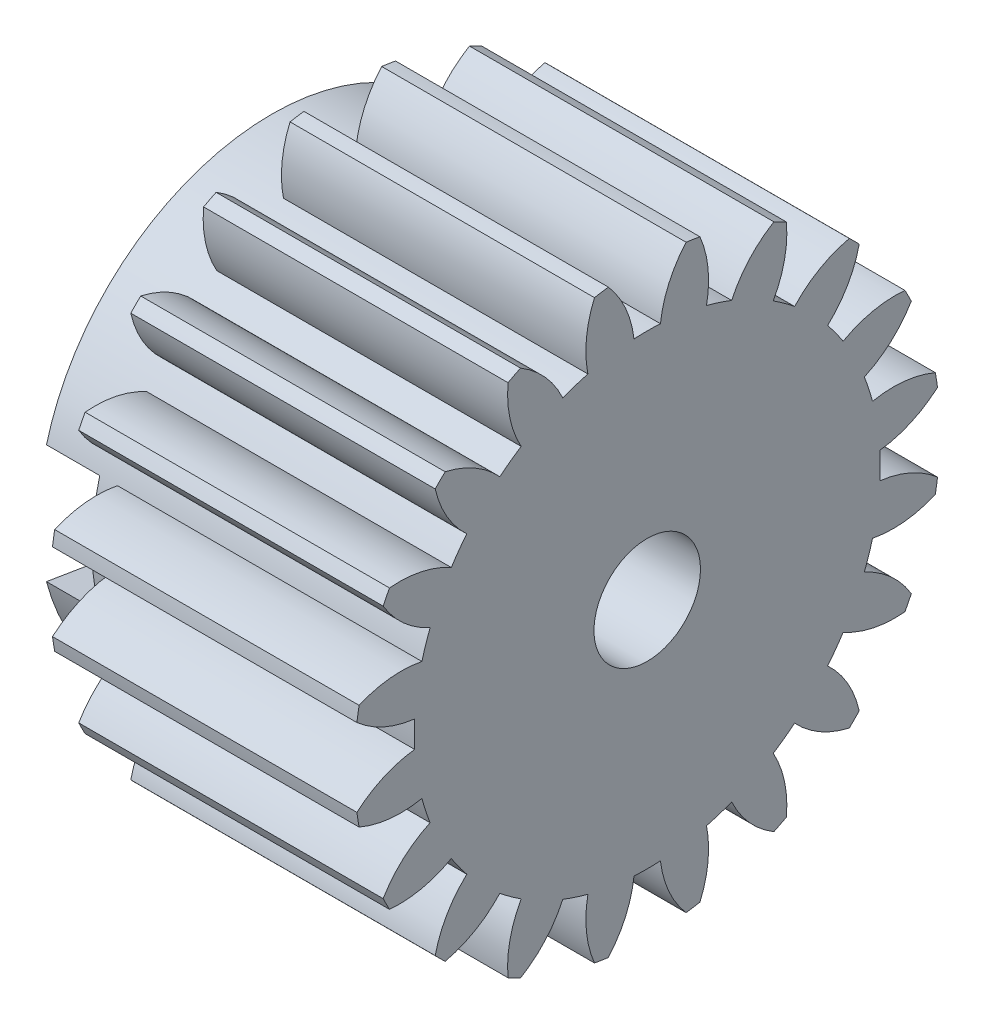
SolidWorks part; units mm, degrees
ref_plane "Plane1" through (0, 0, 0) normal (0, 0, 1) x (1, 0, 0)
ref_plane "Plane2" through (0, 0, 0) normal (0, 1, 0) x (1, 0, 0)
ref_plane "Plane3" through (0, 0, 0) normal (1, 0, 0) x (0, 0, -1)
other "Configuration Table"
sketch "HoldingSke" plane through (0, 0, 0) normal (0, 1, 0) x (1, 0, 0)
  line L0 (0, 0) -> (0.6265, -0.228)
  line L1 (-15, 0) -> (100, 0) construction
  line L2 (0, 0) -> (-2.1039, 2.3779)
  line L3 (0, 0) -> (-11.863, 4.5341)
  line L4 (0, 0) -> (8.1152, 2.9537)
  line L5 (0, 0) -> (-14.9912, -5.5913)
  line L6 (0, 0) -> (-8.2896, -5.593)
  line L7 (-2.1039, 2.3779) -> (1.3401, 18.0029)
  line L8 (-76.2, 54.61) -> (-76.1, 54.61)
  line L9 (-71.009, 38.7566) -> (-53.1078, 45.2721)
  line L10 (-76.2, 71.12) -> (104.1128, 71.12)
  line L11 (0, 0) -> (-10, 0)
  line L12 (-76.2, 101.6) -> (-76.147, 101.6)
  line L13 (24.9733, 27.94) -> (52.9518, 28.4284)
  line L14 (24.9733, 27.94) -> (24.9743, 27.94)
  line L15 (24.9733, 27.94) -> (100.4006, 29.5858)
  line L16 (-63.627, -1.5) -> (-12.827, -1.5)
  circle A0 centre (0, 0) radius 0.4
  circle A1 centre (0, 0) radius 13.124
  circle A2 centre (0, 0) radius 25
  circle A3 centre (0, 0) radius 0.4
  dimension "MHD" = 26.248
  dimension "Hub_dia" = 50
  dimension "Bore" = 0.8
  dimension "MBD" = 0.8
  dimension "Num_teeth" = 20
  dimension "Pitch" = 0.6667
  dimension "Overall_len" = 16
  dimension "Show_teeth" = 20
  dimension "Thickness" = 10
  dimension "OAL" = 16.0001
  dimension "T_dim" = 0.1
  dimension "Ap" = 20
  dimension "H" = 19.05
  dimension "Pitch_radius" = 180.3128
  dimension "Width" = 10
  dimension "Backlash" = 0.053
  dimension "Addendum_fac" = 1
  dimension "Dedendum_fac" = 1.25
  dimension "Clearance_fac" = 0.25
  dimension "Dedendum_add" = 0.001
  dimension "Module" = 1.5
sketch "BasProSke" plane through (0, 0, 0) normal (0, 1, 0) x (1, 0, 0)
  line L0 (-10, 0) -> (60, 0) construction
  line L1 (0, 0) -> (0, 16.5)
  line L2 (0, 0) -> (10, 0)
  line L3 (10, 0) -> (10, 16.5)
  line L4 (10, 16.5) -> (0, 16.5)
  dimension "Thickness" = 10
  dimension "Diameter" = 33
revolve "Base-Revolve" add sketch "BasProSke" angle 360 about L0
sketch "TooCutSke" plane through (0, 0, 0) normal (1, 0, 0) x (0, 0, -1)
  line L1 (0, 0) -> (0, 107) construction
  line L2 (0, 0) -> (-1.2696, 14.9462) construction
  line L3 (0, 0) -> (-4.6808, 29.5532) construction
  line L4 (-1.2696, 14.9462) -> (-2.3404, 14.7766) construction
  arc A0 (0.7438, 13.1029) -> (-0.7438, 13.1029) centre (0, 0) ccw
  arc A1 (2.21, 16.377) -> (-2.21, 16.377) centre (0, 0) ccw
  circle A2 centre (0, 0) radius 15 construction
  circle A3 centre (0, 0) radius 14.0954 construction
  arc A4 (-0.7438, 13.1029) -> (-2.21, 16.377) centre (-6.7025, 12.3999) ccw
  arc A5 (2.21, 16.377) -> (0.7438, 13.1029) centre (6.7025, 12.3999) ccw
  dimension "Root_dia" = 26.248
  dimension "Overcut_dia" = 33.0508
  dimension "Pitch_dia" = 30
  dimension "Base_dia" = 28.1908
  dimension "Flank_rad" = 6
  dimension "Half_ang" = 9
  dimension "Half_CT" = 1.0841
extrude "ToothCut" cut sketch "TooCutSke" along normal through all
fillet "Breaks" [suppressed] radius 0.03
fillet "RootFillets" [suppressed] radius 0.376
pattern_circular "TeethCuts" count 20 every 18 about axis through (-10, 0, 0) along (1, 0, 0) of "ToothCut", "RootFillets", "Breaks"
sketch "HubNeaOneSke" plane through (0, 0, 0) normal (-1, 0, 0) x (0, 0, 1)
  circle A0 centre (0, 0) radius 13.124
  dimension "Diameter" = 26.248
extrude "HubNearOne" add sketch "HubNeaOneSke" along normal blind 6.0001
sketch "HubNeaBotSke" plane through (0, 0, 0) normal (-1, 0, 0) x (0, 0, 1)
  circle A0 centre (0, 0) radius 13.124
  dimension "Diameter" = 26.248
extrude "HubNearBoth" [suppressed] add sketch "HubNeaBotSke" along normal blind 3
ref_plane "FarPln" through (10, 0, 0) normal (1, 0, 0) x (0, 0, -1)
sketch "HubFarSke" plane through (10, 0, 0) normal (1, 0, 0) x (0, 0, -1)
  circle A0 centre (0, 0) radius 13.124
  dimension "Diameter" = 26.248
extrude "HubFar" [suppressed] add sketch "HubFarSke" along normal blind 3
sketch "BorSke" plane through (0, 0, 0) normal (1, 0, 0) x (0, 0, -1)
  circle A0 centre (0, 0) radius 0.4
  dimension "Diameter" = 0.8
extrude "Bore" cut sketch "BorSke" along normal mid plane 32.0001
sketch "KeySke" plane through (0, 0, 0) normal (1, 0, 0) x (0, 0, -1)
  line L0 (-0.05, 0) -> (-0.05, 0.5)
  line L1 (-0.05, 0.5) -> (0.05, 0.5)
  line L2 (0.05, 0.5) -> (0.05, 0)
  line L3 (0, 0) -> (0, 34) construction
  line L4 (-0.05, 0) -> (0.05, 0)
  dimension "Offset" = 0.5
  dimension "Width" = 0.1
extrude "Keyway" [suppressed] cut sketch "KeySke" along normal mid plane 32.0001
pattern_circular "Keyway2" [suppressed] count 2 every 90 about axis through (-10, 0, 0) along (1, 0, 0)
sketch "Sketch1" plane through (-6.0001, 0, 0) normal (-1, 0, 0) x (0, 0, 1)
  line L0 (0, 0) -> (31.5508, 0) construction
  line L1 (15.95, 2.8) -> (4.4173, 4.7)
  line L2 (15.95, -2.8) -> (4.4173, -4.7)
  line L3 (0, 10.0438) -> (0, -22.686) construction
  line L4 (-15.95, -2.8) -> (-4.4173, -4.7)
  line L5 (-15.95, 2.8) -> (-4.4173, 4.7)
  arc A0 (4.4173, 4.7) -> (-4.4173, 4.7) centre (0, 0) ccw
  circle A1 centre (0, 0) radius 4.25 construction
  arc A2 (15.95, -2.8) -> (15.95, 2.8) centre (15.95, 0) ccw
  arc A3 (-15.95, -2.8) -> (-15.95, 2.8) centre (-15.95, 0) cw
  arc A4 (-4.4173, -4.7) -> (4.4173, -4.7) centre (0, 0) ccw
  point P6 (4.25, 0)
  point P7 (18.75, 0)
  point P8 (4.4173, 4.7)
  point P9 (4.4173, -4.7)
  dimension "D1" = 8.5
  dimension "12.5" = 12.9
  dimension "D2" = 5.6
  dimension "D3" = 14.5
  dimension "D4" = 9.4
extrude "Cut-Extrude1" cut sketch "Sketch1" against normal blind 5
sketch "Sketch2" plane through (10, 0, 0) normal (1, 0, 0) x (0, 0, -1)
  arc A80 (-16.354, 2.1898) -> (-13.1029, 0.7438) centre (-12.3999, 6.7025) ccw
  arc A81 (-13.1029, 0.7438) -> (-13.1029, -0.7438) centre (0, 0) ccw
  arc A82 (-13.1029, -0.7438) -> (-16.354, -2.1898) centre (-12.3999, -6.7025) ccw
  arc A83 (-16.354, -2.1898) -> (-16.2303, -2.9711) centre (0, 0) ccw
  arc A84 (-16.2303, -2.9711) -> (-12.6915, -3.3416) centre (-13.8642, 2.5427) ccw
  arc A85 (-12.6915, -3.3416) -> (-12.2318, -4.7564) centre (0, 0) ccw
  arc A86 (-12.2318, -4.7564) -> (-14.8769, -7.1363) centre (-9.7218, -10.2062) ccw
  arc A87 (-14.8769, -7.1363) -> (-14.5178, -7.8411) centre (0, 0) ccw
  arc A88 (-14.5178, -7.8411) -> (-11.0377, -7.0999) centre (-13.9713, -1.866) ccw
  arc A89 (-11.0377, -7.0999) -> (-10.1633, -8.3035) centre (0, 0) ccw
  arc A90 (-10.1633, -8.3035) -> (-11.9436, -11.3842) centre (-6.0921, -12.7109) ccw
  arc A91 (-11.9436, -11.3842) -> (-11.3842, -11.9436) centre (0, 0) ccw
  arc A92 (-11.3842, -11.9436) -> (-8.3035, -10.1633) centre (-12.7109, -6.0921) ccw
  arc A93 (-8.3035, -10.1633) -> (-7.0999, -11.0377) centre (0, 0) ccw
  arc A94 (-7.0999, -11.0377) -> (-7.8411, -14.5178) centre (-1.866, -13.9713) ccw
  arc A95 (-7.8411, -14.5178) -> (-7.1363, -14.8769) centre (0, 0) ccw
  arc A96 (-7.1363, -14.8769) -> (-4.7564, -12.2318) centre (-10.2062, -9.7218) ccw
  arc A97 (-4.7564, -12.2318) -> (-3.3416, -12.6915) centre (0, 0) ccw
  arc A98 (-3.3416, -12.6915) -> (-2.9711, -16.2303) centre (2.5427, -13.8642) ccw
  arc A99 (-2.9711, -16.2303) -> (-2.1898, -16.354) centre (0, 0) ccw
  arc A100 (-2.1898, -16.354) -> (-0.7438, -13.1029) centre (-6.7025, -12.3999) ccw
  arc A101 (-0.7438, -13.1029) -> (0.7438, -13.1029) centre (0, 0) ccw
  arc A102 (0.7438, -13.1029) -> (2.1898, -16.354) centre (6.7025, -12.3999) ccw
  arc A103 (2.1898, -16.354) -> (2.9711, -16.2303) centre (0, 0) ccw
  arc A104 (2.9711, -16.2303) -> (3.3416, -12.6915) centre (-2.5427, -13.8642) ccw
  arc A105 (3.3416, -12.6915) -> (4.7564, -12.2318) centre (0, 0) ccw
  arc A106 (4.7564, -12.2318) -> (7.1363, -14.8769) centre (10.2062, -9.7218) ccw
  arc A107 (7.1363, -14.8769) -> (7.8411, -14.5178) centre (0, 0) ccw
  arc A108 (7.8411, -14.5178) -> (7.0999, -11.0377) centre (1.866, -13.9713) ccw
  arc A109 (7.0999, -11.0377) -> (8.3035, -10.1633) centre (0, 0) ccw
  arc A110 (8.3035, -10.1633) -> (11.3842, -11.9436) centre (12.7109, -6.0921) ccw
  arc A111 (11.3842, -11.9436) -> (11.9436, -11.3842) centre (0, 0) ccw
  arc A112 (11.9436, -11.3842) -> (10.1633, -8.3035) centre (6.0921, -12.7109) ccw
  arc A113 (10.1633, -8.3035) -> (11.0377, -7.0999) centre (0, 0) ccw
  arc A114 (11.0377, -7.0999) -> (14.5178, -7.8411) centre (13.9713, -1.866) ccw
  arc A115 (14.5178, -7.8411) -> (14.8769, -7.1363) centre (0, 0) ccw
  arc A116 (14.8769, -7.1363) -> (12.2318, -4.7564) centre (9.7218, -10.2062) ccw
  arc A117 (12.2318, -4.7564) -> (12.6915, -3.3416) centre (0, 0) ccw
  arc A118 (12.6915, -3.3416) -> (16.2303, -2.9711) centre (13.8642, 2.5427) ccw
  arc A119 (16.2303, -2.9711) -> (16.354, -2.1898) centre (0, 0) ccw
  arc A120 (16.354, -2.1898) -> (13.1029, -0.7438) centre (12.3999, -6.7025) ccw
  arc A121 (13.1029, -0.7438) -> (13.1029, 0.7438) centre (0, 0) ccw
  arc A122 (13.1029, 0.7438) -> (16.354, 2.1898) centre (12.3999, 6.7025) ccw
  arc A123 (16.354, 2.1898) -> (16.2303, 2.9711) centre (0, 0) ccw
  arc A124 (16.2303, 2.9711) -> (12.6915, 3.3416) centre (13.8642, -2.5427) ccw
  arc A125 (12.6915, 3.3416) -> (12.2318, 4.7564) centre (0, 0) ccw
  arc A126 (12.2318, 4.7564) -> (14.8769, 7.1363) centre (9.7218, 10.2062) ccw
  arc A127 (14.8769, 7.1363) -> (14.5178, 7.8411) centre (0, 0) ccw
  arc A128 (14.5178, 7.8411) -> (11.0377, 7.0999) centre (13.9713, 1.866) ccw
  arc A129 (11.0377, 7.0999) -> (10.1633, 8.3035) centre (0, 0) ccw
  arc A130 (10.1633, 8.3035) -> (11.9436, 11.3842) centre (6.0921, 12.7109) ccw
  arc A131 (11.9436, 11.3842) -> (11.3842, 11.9436) centre (0, 0) ccw
  arc A132 (11.3842, 11.9436) -> (8.3035, 10.1633) centre (12.7109, 6.0921) ccw
  arc A133 (8.3035, 10.1633) -> (7.0999, 11.0377) centre (0, 0) ccw
  arc A134 (7.0999, 11.0377) -> (7.8411, 14.5178) centre (1.866, 13.9713) ccw
  arc A135 (7.8411, 14.5178) -> (7.1363, 14.8769) centre (0, 0) ccw
  arc A136 (7.1363, 14.8769) -> (4.7564, 12.2318) centre (10.2062, 9.7218) ccw
  arc A137 (4.7564, 12.2318) -> (3.3416, 12.6915) centre (0, 0) ccw
  arc A138 (3.3416, 12.6915) -> (2.9711, 16.2303) centre (-2.5427, 13.8642) ccw
  arc A139 (2.9711, 16.2303) -> (2.1898, 16.354) centre (0, 0) ccw
  arc A140 (2.1898, 16.354) -> (0.7438, 13.1029) centre (6.7025, 12.3999) ccw
  arc A141 (0.7438, 13.1029) -> (-0.7438, 13.1029) centre (0, 0) ccw
  arc A142 (-0.7438, 13.1029) -> (-2.1898, 16.354) centre (-6.7025, 12.3999) ccw
  arc A143 (-2.1898, 16.354) -> (-2.9711, 16.2303) centre (0, 0) ccw
  arc A144 (-2.9711, 16.2303) -> (-3.3416, 12.6915) centre (2.5427, 13.8642) ccw
  arc A145 (-3.3416, 12.6915) -> (-4.7564, 12.2318) centre (0, 0) ccw
  arc A146 (-4.7564, 12.2318) -> (-7.1363, 14.8769) centre (-10.2062, 9.7218) ccw
  arc A147 (-7.1363, 14.8769) -> (-7.8411, 14.5178) centre (0, 0) ccw
  arc A148 (-7.8411, 14.5178) -> (-7.0999, 11.0377) centre (-1.866, 13.9713) ccw
  arc A149 (-7.0999, 11.0377) -> (-8.3035, 10.1633) centre (0, 0) ccw
  arc A150 (-8.3035, 10.1633) -> (-11.3842, 11.9436) centre (-12.7109, 6.0921) ccw
  arc A151 (-11.3842, 11.9436) -> (-11.9436, 11.3842) centre (0, 0) ccw
  arc A152 (-11.9436, 11.3842) -> (-10.1633, 8.3035) centre (-6.0921, 12.7109) ccw
  arc A153 (-10.1633, 8.3035) -> (-11.0377, 7.0999) centre (0, 0) ccw
  arc A154 (-11.0377, 7.0999) -> (-14.5178, 7.8411) centre (-13.9713, 1.866) ccw
  arc A155 (-14.5178, 7.8411) -> (-14.8769, 7.1363) centre (0, 0) ccw
  arc A156 (-14.8769, 7.1363) -> (-12.2318, 4.7564) centre (-9.7218, 10.2062) ccw
  arc A157 (-12.2318, 4.7564) -> (-12.6915, 3.3416) centre (0, 0) ccw
  arc A158 (-12.6915, 3.3416) -> (-16.2303, 2.9711) centre (-13.8642, -2.5427) ccw
  arc A159 (-16.2303, 2.9711) -> (-16.354, 2.1898) centre (0, 0) ccw
  arc A160 (-16.354, 2.1898) -> (-13.1029, 0.7438) centre (-12.3999, 6.7025) ccw
  arc A161 (-13.1029, 0.7438) -> (-13.1029, -0.7438) centre (0, 0) ccw
  arc A162 (-13.1029, -0.7438) -> (-16.354, -2.1898) centre (-12.3999, -6.7025) ccw
  arc A163 (-16.354, -2.1898) -> (-16.2303, -2.9711) centre (0, 0) ccw
  arc A164 (-16.2303, -2.9711) -> (-12.6915, -3.3416) centre (-13.8642, 2.5427) ccw
  arc A165 (-12.6915, -3.3416) -> (-12.2318, -4.7564) centre (0, 0) ccw
  arc A166 (-12.2318, -4.7564) -> (-14.8769, -7.1363) centre (-9.7218, -10.2062) ccw
  arc A167 (-14.8769, -7.1363) -> (-14.5178, -7.8411) centre (0, 0) ccw
  arc A168 (-14.5178, -7.8411) -> (-11.0377, -7.0999) centre (-13.9713, -1.866) ccw
  arc A169 (-11.0377, -7.0999) -> (-10.1633, -8.3035) centre (0, 0) ccw
  arc A170 (-10.1633, -8.3035) -> (-11.9436, -11.3842) centre (-6.0921, -12.7109) ccw
  arc A171 (-11.9436, -11.3842) -> (-11.3842, -11.9436) centre (0, 0) ccw
  arc A172 (-11.3842, -11.9436) -> (-8.3035, -10.1633) centre (-12.7109, -6.0921) ccw
  arc A173 (-8.3035, -10.1633) -> (-7.0999, -11.0377) centre (0, 0) ccw
  arc A174 (-7.0999, -11.0377) -> (-7.8411, -14.5178) centre (-1.866, -13.9713) ccw
  arc A175 (-7.8411, -14.5178) -> (-7.1363, -14.8769) centre (0, 0) ccw
  arc A176 (-7.1363, -14.8769) -> (-4.7564, -12.2318) centre (-10.2062, -9.7218) ccw
  arc A177 (-4.7564, -12.2318) -> (-3.3416, -12.6915) centre (0, 0) ccw
  arc A178 (-3.3416, -12.6915) -> (-2.9711, -16.2303) centre (2.5427, -13.8642) ccw
  arc A179 (-2.9711, -16.2303) -> (-2.1898, -16.354) centre (0, 0) ccw
  arc A180 (-2.1898, -16.354) -> (-0.7438, -13.1029) centre (-6.7025, -12.3999) ccw
  arc A181 (-0.7438, -13.1029) -> (0.7438, -13.1029) centre (0, 0) ccw
  arc A182 (0.7438, -13.1029) -> (2.1898, -16.354) centre (6.7025, -12.3999) ccw
  arc A183 (2.1898, -16.354) -> (2.9711, -16.2303) centre (0, 0) ccw
  arc A184 (2.9711, -16.2303) -> (3.3416, -12.6915) centre (-2.5427, -13.8642) ccw
  arc A185 (3.3416, -12.6915) -> (4.7564, -12.2318) centre (0, 0) ccw
  arc A186 (4.7564, -12.2318) -> (7.1363, -14.8769) centre (10.2062, -9.7218) ccw
  arc A187 (7.1363, -14.8769) -> (7.8411, -14.5178) centre (0, 0) ccw
  arc A188 (7.8411, -14.5178) -> (7.0999, -11.0377) centre (1.866, -13.9713) ccw
  arc A189 (7.0999, -11.0377) -> (8.3035, -10.1633) centre (0, 0) ccw
  arc A190 (8.3035, -10.1633) -> (11.3842, -11.9436) centre (12.7109, -6.0921) ccw
  arc A191 (11.3842, -11.9436) -> (11.9436, -11.3842) centre (0, 0) ccw
  arc A192 (11.9436, -11.3842) -> (10.1633, -8.3035) centre (6.0921, -12.7109) ccw
  arc A193 (10.1633, -8.3035) -> (11.0377, -7.0999) centre (0, 0) ccw
  arc A194 (11.0377, -7.0999) -> (14.5178, -7.8411) centre (13.9713, -1.866) ccw
  arc A195 (14.5178, -7.8411) -> (14.8769, -7.1363) centre (0, 0) ccw
  arc A196 (14.8769, -7.1363) -> (12.2318, -4.7564) centre (9.7218, -10.2062) ccw
  arc A197 (12.2318, -4.7564) -> (12.6915, -3.3416) centre (0, 0) ccw
  arc A198 (12.6915, -3.3416) -> (16.2303, -2.9711) centre (13.8642, 2.5427) ccw
  arc A199 (16.2303, -2.9711) -> (16.354, -2.1898) centre (0, 0) ccw
  arc A200 (16.354, -2.1898) -> (13.1029, -0.7438) centre (12.3999, -6.7025) ccw
  arc A201 (13.1029, -0.7438) -> (13.1029, 0.7438) centre (0, 0) ccw
  arc A202 (13.1029, 0.7438) -> (16.354, 2.1898) centre (12.3999, 6.7025) ccw
  arc A203 (16.354, 2.1898) -> (16.2303, 2.9711) centre (0, 0) ccw
  arc A204 (16.2303, 2.9711) -> (12.6915, 3.3416) centre (13.8642, -2.5427) ccw
  arc A205 (12.6915, 3.3416) -> (12.2318, 4.7564) centre (0, 0) ccw
  arc A206 (12.2318, 4.7564) -> (14.8769, 7.1363) centre (9.7218, 10.2062) ccw
  arc A207 (14.8769, 7.1363) -> (14.5178, 7.8411) centre (0, 0) ccw
  arc A208 (14.5178, 7.8411) -> (11.0377, 7.0999) centre (13.9713, 1.866) ccw
  arc A209 (11.0377, 7.0999) -> (10.1633, 8.3035) centre (0, 0) ccw
  arc A210 (10.1633, 8.3035) -> (11.9436, 11.3842) centre (6.0921, 12.7109) ccw
  arc A211 (11.9436, 11.3842) -> (11.3842, 11.9436) centre (0, 0) ccw
  arc A212 (11.3842, 11.9436) -> (8.3035, 10.1633) centre (12.7109, 6.0921) ccw
  arc A213 (8.3035, 10.1633) -> (7.0999, 11.0377) centre (0, 0) ccw
  arc A214 (7.0999, 11.0377) -> (7.8411, 14.5178) centre (1.866, 13.9713) ccw
  arc A215 (7.8411, 14.5178) -> (7.1363, 14.8769) centre (0, 0) ccw
  arc A216 (7.1363, 14.8769) -> (4.7564, 12.2318) centre (10.2062, 9.7218) ccw
  arc A217 (4.7564, 12.2318) -> (3.3416, 12.6915) centre (0, 0) ccw
  arc A218 (3.3416, 12.6915) -> (2.9711, 16.2303) centre (-2.5427, 13.8642) ccw
  arc A219 (2.9711, 16.2303) -> (2.1898, 16.354) centre (0, 0) ccw
  arc A220 (2.1898, 16.354) -> (0.7438, 13.1029) centre (6.7025, 12.3999) ccw
  arc A221 (0.7438, 13.1029) -> (-0.7438, 13.1029) centre (0, 0) ccw
  arc A222 (-0.7438, 13.1029) -> (-2.1898, 16.354) centre (-6.7025, 12.3999) ccw
  arc A223 (-2.1898, 16.354) -> (-2.9711, 16.2303) centre (0, 0) ccw
  arc A224 (-2.9711, 16.2303) -> (-3.3416, 12.6915) centre (2.5427, 13.8642) ccw
  arc A225 (-3.3416, 12.6915) -> (-4.7564, 12.2318) centre (0, 0) ccw
  arc A226 (-4.7564, 12.2318) -> (-7.1363, 14.8769) centre (-10.2062, 9.7218) ccw
  arc A227 (-7.1363, 14.8769) -> (-7.8411, 14.5178) centre (0, 0) ccw
  arc A228 (-7.8411, 14.5178) -> (-7.0999, 11.0377) centre (-1.866, 13.9713) ccw
  arc A229 (-7.0999, 11.0377) -> (-8.3035, 10.1633) centre (0, 0) ccw
  arc A230 (-8.3035, 10.1633) -> (-11.3842, 11.9436) centre (-12.7109, 6.0921) ccw
  arc A231 (-11.3842, 11.9436) -> (-11.9436, 11.3842) centre (0, 0) ccw
  arc A232 (-11.9436, 11.3842) -> (-10.1633, 8.3035) centre (-6.0921, 12.7109) ccw
  arc A233 (-10.1633, 8.3035) -> (-11.0377, 7.0999) centre (0, 0) ccw
  arc A234 (-11.0377, 7.0999) -> (-14.5178, 7.8411) centre (-13.9713, 1.866) ccw
  arc A235 (-14.5178, 7.8411) -> (-14.8769, 7.1363) centre (0, 0) ccw
  arc A236 (-14.8769, 7.1363) -> (-12.2318, 4.7564) centre (-9.7218, 10.2062) ccw
  arc A237 (-12.2318, 4.7564) -> (-12.6915, 3.3416) centre (0, 0) ccw
  arc A238 (-12.6915, 3.3416) -> (-16.2303, 2.9711) centre (-13.8642, -2.5427) ccw
  arc A239 (-16.2303, 2.9711) -> (-16.354, 2.1898) centre (0, 0) ccw
  dimension "D1" = 0
extrude "Boss-Extrude1" add sketch "Sketch2" along normal blind 7.15 contours A160 A161 A162 A163 A164 A165 A166 A167 A168 A169 A170 A171 A172 A173 A174 A175 A176 A177 A178 A179 A180 A181 A182 A183 A184 A185 A186 A187 A188 A189 A190 A191 A192 A193 A194 A195 A196 A197 A198 A199 A200 A201 A202 A203 A204 A205 A206 A207 A208 A209 A210 A211 A212 A213 A214 A215 A216 A217 A218 A219 A220 A221 A222 A223 A224 A225 A226 A227 A228 A229 A230 A231 A232 A233 A234 A235 A236 A237 A238 A239
sketch "Sketch4" plane through (-6.0001, 0, 0) normal (-1, 0, 0) x (0, 0, 1)
  circle A0 centre (0, 0) radius 13.124
extrude "Cut-Extrude2" cut sketch "Sketch4" against normal blind 2
sketch "Sketch5" plane through (17.15, 0, 0) normal (1, 0, 0) x (0, 0, -1)
  arc A80 (-16.2303, 2.9711) -> (-16.354, 2.1898) centre (0, 0) ccw
  arc A81 (-16.354, 2.1898) -> (-13.1029, 0.7438) centre (-12.3999, 6.7025) ccw
  arc A82 (-13.1029, 0.7438) -> (-13.1029, -0.7438) centre (0, 0) ccw
  arc A83 (-13.1029, -0.7438) -> (-16.354, -2.1898) centre (-12.3999, -6.7025) ccw
  arc A84 (-16.354, -2.1898) -> (-16.2303, -2.9711) centre (0, 0) ccw
  arc A85 (-16.2303, -2.9711) -> (-12.6915, -3.3416) centre (-13.8642, 2.5427) ccw
  arc A86 (-12.6915, -3.3416) -> (-12.2318, -4.7564) centre (0, 0) ccw
  arc A87 (-12.2318, -4.7564) -> (-14.8769, -7.1363) centre (-9.7218, -10.2062) ccw
  arc A88 (-14.8769, -7.1363) -> (-14.5178, -7.8411) centre (0, 0) ccw
  arc A89 (-14.5178, -7.8411) -> (-11.0377, -7.0999) centre (-13.9713, -1.866) ccw
  arc A90 (-11.0377, -7.0999) -> (-10.1633, -8.3035) centre (0, 0) ccw
  arc A91 (-10.1633, -8.3035) -> (-11.9436, -11.3842) centre (-6.0921, -12.7109) ccw
  arc A92 (-11.9436, -11.3842) -> (-11.3842, -11.9436) centre (0, 0) ccw
  arc A93 (-11.3842, -11.9436) -> (-8.3035, -10.1633) centre (-12.7109, -6.0921) ccw
  arc A94 (-8.3035, -10.1633) -> (-7.0999, -11.0377) centre (0, 0) ccw
  arc A95 (-7.0999, -11.0377) -> (-7.8411, -14.5178) centre (-1.866, -13.9713) ccw
  arc A96 (-7.8411, -14.5178) -> (-7.1363, -14.8769) centre (0, 0) ccw
  arc A97 (-7.1363, -14.8769) -> (-4.7564, -12.2318) centre (-10.2062, -9.7218) ccw
  arc A98 (-4.7564, -12.2318) -> (-3.3416, -12.6915) centre (0, 0) ccw
  arc A99 (-3.3416, -12.6915) -> (-2.9711, -16.2303) centre (2.5427, -13.8642) ccw
  arc A100 (-2.9711, -16.2303) -> (-2.1898, -16.354) centre (0, 0) ccw
  arc A101 (-2.1898, -16.354) -> (-0.7438, -13.1029) centre (-6.7025, -12.3999) ccw
  arc A102 (-0.7438, -13.1029) -> (0.7438, -13.1029) centre (0, 0) ccw
  arc A103 (0.7438, -13.1029) -> (2.1898, -16.354) centre (6.7025, -12.3999) ccw
  arc A104 (2.1898, -16.354) -> (2.9711, -16.2303) centre (0, 0) ccw
  arc A105 (2.9711, -16.2303) -> (3.3416, -12.6915) centre (-2.5427, -13.8642) ccw
  arc A106 (3.3416, -12.6915) -> (4.7564, -12.2318) centre (0, 0) ccw
  arc A107 (4.7564, -12.2318) -> (7.1363, -14.8769) centre (10.2062, -9.7218) ccw
  arc A108 (7.1363, -14.8769) -> (7.8411, -14.5178) centre (0, 0) ccw
  arc A109 (7.8411, -14.5178) -> (7.0999, -11.0377) centre (1.866, -13.9713) ccw
  arc A110 (7.0999, -11.0377) -> (8.3035, -10.1633) centre (0, 0) ccw
  arc A111 (8.3035, -10.1633) -> (11.3842, -11.9436) centre (12.7109, -6.0921) ccw
  arc A112 (11.3842, -11.9436) -> (11.9436, -11.3842) centre (0, 0) ccw
  arc A113 (11.9436, -11.3842) -> (10.1633, -8.3035) centre (6.0921, -12.7109) ccw
  arc A114 (10.1633, -8.3035) -> (11.0377, -7.0999) centre (0, 0) ccw
  arc A115 (11.0377, -7.0999) -> (14.5178, -7.8411) centre (13.9713, -1.866) ccw
  arc A116 (14.5178, -7.8411) -> (14.8769, -7.1363) centre (0, 0) ccw
  arc A117 (14.8769, -7.1363) -> (12.2318, -4.7564) centre (9.7218, -10.2062) ccw
  arc A118 (12.2318, -4.7564) -> (12.6915, -3.3416) centre (0, 0) ccw
  arc A119 (12.6915, -3.3416) -> (16.2303, -2.9711) centre (13.8642, 2.5427) ccw
  arc A120 (16.2303, -2.9711) -> (16.354, -2.1898) centre (0, 0) ccw
  arc A121 (16.354, -2.1898) -> (13.1029, -0.7438) centre (12.3999, -6.7025) ccw
  arc A122 (13.1029, -0.7438) -> (13.1029, 0.7438) centre (0, 0) ccw
  arc A123 (13.1029, 0.7438) -> (16.354, 2.1898) centre (12.3999, 6.7025) ccw
  arc A124 (16.354, 2.1898) -> (16.2303, 2.9711) centre (0, 0) ccw
  arc A125 (16.2303, 2.9711) -> (12.6915, 3.3416) centre (13.8642, -2.5427) ccw
  arc A126 (12.6915, 3.3416) -> (12.2318, 4.7564) centre (0, 0) ccw
  arc A127 (12.2318, 4.7564) -> (14.8769, 7.1363) centre (9.7218, 10.2062) ccw
  arc A128 (14.8769, 7.1363) -> (14.5178, 7.8411) centre (0, 0) ccw
  arc A129 (14.5178, 7.8411) -> (11.0377, 7.0999) centre (13.9713, 1.866) ccw
  arc A130 (11.0377, 7.0999) -> (10.1633, 8.3035) centre (0, 0) ccw
  arc A131 (10.1633, 8.3035) -> (11.9436, 11.3842) centre (6.0921, 12.7109) ccw
  arc A132 (11.9436, 11.3842) -> (11.3842, 11.9436) centre (0, 0) ccw
  arc A133 (11.3842, 11.9436) -> (8.3035, 10.1633) centre (12.7109, 6.0921) ccw
  arc A134 (8.3035, 10.1633) -> (7.0999, 11.0377) centre (0, 0) ccw
  arc A135 (7.0999, 11.0377) -> (7.8411, 14.5178) centre (1.866, 13.9713) ccw
  arc A136 (7.8411, 14.5178) -> (7.1363, 14.8769) centre (0, 0) ccw
  arc A137 (7.1363, 14.8769) -> (4.7564, 12.2318) centre (10.2062, 9.7218) ccw
  arc A138 (4.7564, 12.2318) -> (3.3416, 12.6915) centre (0, 0) ccw
  arc A139 (3.3416, 12.6915) -> (2.9711, 16.2303) centre (-2.5427, 13.8642) ccw
  arc A140 (2.9711, 16.2303) -> (2.1898, 16.354) centre (0, 0) ccw
  arc A141 (2.1898, 16.354) -> (0.7438, 13.1029) centre (6.7025, 12.3999) ccw
  arc A142 (0.7438, 13.1029) -> (-0.7438, 13.1029) centre (0, 0) ccw
  arc A143 (-0.7438, 13.1029) -> (-2.1898, 16.354) centre (-6.7025, 12.3999) ccw
  arc A144 (-2.1898, 16.354) -> (-2.9711, 16.2303) centre (0, 0) ccw
  arc A145 (-2.9711, 16.2303) -> (-3.3416, 12.6915) centre (2.5427, 13.8642) ccw
  arc A146 (-3.3416, 12.6915) -> (-4.7564, 12.2318) centre (0, 0) ccw
  arc A147 (-4.7564, 12.2318) -> (-7.1363, 14.8769) centre (-10.2062, 9.7218) ccw
  arc A148 (-7.1363, 14.8769) -> (-7.8411, 14.5178) centre (0, 0) ccw
  arc A149 (-7.8411, 14.5178) -> (-7.0999, 11.0377) centre (-1.866, 13.9713) ccw
  arc A150 (-7.0999, 11.0377) -> (-8.3035, 10.1633) centre (0, 0) ccw
  arc A151 (-8.3035, 10.1633) -> (-11.3842, 11.9436) centre (-12.7109, 6.0921) ccw
  arc A152 (-11.3842, 11.9436) -> (-11.9436, 11.3842) centre (0, 0) ccw
  arc A153 (-11.9436, 11.3842) -> (-10.1633, 8.3035) centre (-6.0921, 12.7109) ccw
  arc A154 (-10.1633, 8.3035) -> (-11.0377, 7.0999) centre (0, 0) ccw
  arc A155 (-11.0377, 7.0999) -> (-14.5178, 7.8411) centre (-13.9713, 1.866) ccw
  arc A156 (-14.5178, 7.8411) -> (-14.8769, 7.1363) centre (0, 0) ccw
  arc A157 (-14.8769, 7.1363) -> (-12.2318, 4.7564) centre (-9.7218, 10.2062) ccw
  arc A158 (-12.2318, 4.7564) -> (-12.6915, 3.3416) centre (0, 0) ccw
  arc A159 (-12.6915, 3.3416) -> (-16.2303, 2.9711) centre (-13.8642, -2.5427) ccw
  arc A160 (-16.2303, 2.9711) -> (-16.354, 2.1898) centre (0, 0) ccw
  arc A161 (-16.354, 2.1898) -> (-13.1029, 0.7438) centre (-12.3999, 6.7025) ccw
  arc A162 (-13.1029, 0.7438) -> (-13.1029, -0.7438) centre (0, 0) ccw
  arc A163 (-13.1029, -0.7438) -> (-16.354, -2.1898) centre (-12.3999, -6.7025) ccw
  arc A164 (-16.354, -2.1898) -> (-16.2303, -2.9711) centre (0, 0) ccw
  arc A165 (-16.2303, -2.9711) -> (-12.6915, -3.3416) centre (-13.8642, 2.5427) ccw
  arc A166 (-12.6915, -3.3416) -> (-12.2318, -4.7564) centre (0, 0) ccw
  arc A167 (-12.2318, -4.7564) -> (-14.8769, -7.1363) centre (-9.7218, -10.2062) ccw
  arc A168 (-14.8769, -7.1363) -> (-14.5178, -7.8411) centre (0, 0) ccw
  arc A169 (-14.5178, -7.8411) -> (-11.0377, -7.0999) centre (-13.9713, -1.866) ccw
  arc A170 (-11.0377, -7.0999) -> (-10.1633, -8.3035) centre (0, 0) ccw
  arc A171 (-10.1633, -8.3035) -> (-11.9436, -11.3842) centre (-6.0921, -12.7109) ccw
  arc A172 (-11.9436, -11.3842) -> (-11.3842, -11.9436) centre (0, 0) ccw
  arc A173 (-11.3842, -11.9436) -> (-8.3035, -10.1633) centre (-12.7109, -6.0921) ccw
  arc A174 (-8.3035, -10.1633) -> (-7.0999, -11.0377) centre (0, 0) ccw
  arc A175 (-7.0999, -11.0377) -> (-7.8411, -14.5178) centre (-1.866, -13.9713) ccw
  arc A176 (-7.8411, -14.5178) -> (-7.1363, -14.8769) centre (0, 0) ccw
  arc A177 (-7.1363, -14.8769) -> (-4.7564, -12.2318) centre (-10.2062, -9.7218) ccw
  arc A178 (-4.7564, -12.2318) -> (-3.3416, -12.6915) centre (0, 0) ccw
  arc A179 (-3.3416, -12.6915) -> (-2.9711, -16.2303) centre (2.5427, -13.8642) ccw
  arc A180 (-2.9711, -16.2303) -> (-2.1898, -16.354) centre (0, 0) ccw
  arc A181 (-2.1898, -16.354) -> (-0.7438, -13.1029) centre (-6.7025, -12.3999) ccw
  arc A182 (-0.7438, -13.1029) -> (0.7438, -13.1029) centre (0, 0) ccw
  arc A183 (0.7438, -13.1029) -> (2.1898, -16.354) centre (6.7025, -12.3999) ccw
  arc A184 (2.1898, -16.354) -> (2.9711, -16.2303) centre (0, 0) ccw
  arc A185 (2.9711, -16.2303) -> (3.3416, -12.6915) centre (-2.5427, -13.8642) ccw
  arc A186 (3.3416, -12.6915) -> (4.7564, -12.2318) centre (0, 0) ccw
  arc A187 (4.7564, -12.2318) -> (7.1363, -14.8769) centre (10.2062, -9.7218) ccw
  arc A188 (7.1363, -14.8769) -> (7.8411, -14.5178) centre (0, 0) ccw
  arc A189 (7.8411, -14.5178) -> (7.0999, -11.0377) centre (1.866, -13.9713) ccw
  arc A190 (7.0999, -11.0377) -> (8.3035, -10.1633) centre (0, 0) ccw
  arc A191 (8.3035, -10.1633) -> (11.3842, -11.9436) centre (12.7109, -6.0921) ccw
  arc A192 (11.3842, -11.9436) -> (11.9436, -11.3842) centre (0, 0) ccw
  arc A193 (11.9436, -11.3842) -> (10.1633, -8.3035) centre (6.0921, -12.7109) ccw
  arc A194 (10.1633, -8.3035) -> (11.0377, -7.0999) centre (0, 0) ccw
  arc A195 (11.0377, -7.0999) -> (14.5178, -7.8411) centre (13.9713, -1.866) ccw
  arc A196 (14.5178, -7.8411) -> (14.8769, -7.1363) centre (0, 0) ccw
  arc A197 (14.8769, -7.1363) -> (12.2318, -4.7564) centre (9.7218, -10.2062) ccw
  arc A198 (12.2318, -4.7564) -> (12.6915, -3.3416) centre (0, 0) ccw
  arc A199 (12.6915, -3.3416) -> (16.2303, -2.9711) centre (13.8642, 2.5427) ccw
  arc A200 (16.2303, -2.9711) -> (16.354, -2.1898) centre (0, 0) ccw
  arc A201 (16.354, -2.1898) -> (13.1029, -0.7438) centre (12.3999, -6.7025) ccw
  arc A202 (13.1029, -0.7438) -> (13.1029, 0.7438) centre (0, 0) ccw
  arc A203 (13.1029, 0.7438) -> (16.354, 2.1898) centre (12.3999, 6.7025) ccw
  arc A204 (16.354, 2.1898) -> (16.2303, 2.9711) centre (0, 0) ccw
  arc A205 (16.2303, 2.9711) -> (12.6915, 3.3416) centre (13.8642, -2.5427) ccw
  arc A206 (12.6915, 3.3416) -> (12.2318, 4.7564) centre (0, 0) ccw
  arc A207 (12.2318, 4.7564) -> (14.8769, 7.1363) centre (9.7218, 10.2062) ccw
  arc A208 (14.8769, 7.1363) -> (14.5178, 7.8411) centre (0, 0) ccw
  arc A209 (14.5178, 7.8411) -> (11.0377, 7.0999) centre (13.9713, 1.866) ccw
  arc A210 (11.0377, 7.0999) -> (10.1633, 8.3035) centre (0, 0) ccw
  arc A211 (10.1633, 8.3035) -> (11.9436, 11.3842) centre (6.0921, 12.7109) ccw
  arc A212 (11.9436, 11.3842) -> (11.3842, 11.9436) centre (0, 0) ccw
  arc A213 (11.3842, 11.9436) -> (8.3035, 10.1633) centre (12.7109, 6.0921) ccw
  arc A214 (8.3035, 10.1633) -> (7.0999, 11.0377) centre (0, 0) ccw
  arc A215 (7.0999, 11.0377) -> (7.8411, 14.5178) centre (1.866, 13.9713) ccw
  arc A216 (7.8411, 14.5178) -> (7.1363, 14.8769) centre (0, 0) ccw
  arc A217 (7.1363, 14.8769) -> (4.7564, 12.2318) centre (10.2062, 9.7218) ccw
  arc A218 (4.7564, 12.2318) -> (3.3416, 12.6915) centre (0, 0) ccw
  arc A219 (3.3416, 12.6915) -> (2.9711, 16.2303) centre (-2.5427, 13.8642) ccw
  arc A220 (2.9711, 16.2303) -> (2.1898, 16.354) centre (0, 0) ccw
  arc A221 (2.1898, 16.354) -> (0.7438, 13.1029) centre (6.7025, 12.3999) ccw
  arc A222 (0.7438, 13.1029) -> (-0.7438, 13.1029) centre (0, 0) ccw
  arc A223 (-0.7438, 13.1029) -> (-2.1898, 16.354) centre (-6.7025, 12.3999) ccw
  arc A224 (-2.1898, 16.354) -> (-2.9711, 16.2303) centre (0, 0) ccw
  arc A225 (-2.9711, 16.2303) -> (-3.3416, 12.6915) centre (2.5427, 13.8642) ccw
  arc A226 (-3.3416, 12.6915) -> (-4.7564, 12.2318) centre (0, 0) ccw
  arc A227 (-4.7564, 12.2318) -> (-7.1363, 14.8769) centre (-10.2062, 9.7218) ccw
  arc A228 (-7.1363, 14.8769) -> (-7.8411, 14.5178) centre (0, 0) ccw
  arc A229 (-7.8411, 14.5178) -> (-7.0999, 11.0377) centre (-1.866, 13.9713) ccw
  arc A230 (-7.0999, 11.0377) -> (-8.3035, 10.1633) centre (0, 0) ccw
  arc A231 (-8.3035, 10.1633) -> (-11.3842, 11.9436) centre (-12.7109, 6.0921) ccw
  arc A232 (-11.3842, 11.9436) -> (-11.9436, 11.3842) centre (0, 0) ccw
  arc A233 (-11.9436, 11.3842) -> (-10.1633, 8.3035) centre (-6.0921, 12.7109) ccw
  arc A234 (-10.1633, 8.3035) -> (-11.0377, 7.0999) centre (0, 0) ccw
  arc A235 (-11.0377, 7.0999) -> (-14.5178, 7.8411) centre (-13.9713, 1.866) ccw
  arc A236 (-14.5178, 7.8411) -> (-14.8769, 7.1363) centre (0, 0) ccw
  arc A237 (-14.8769, 7.1363) -> (-12.2318, 4.7564) centre (-9.7218, 10.2062) ccw
  arc A238 (-12.2318, 4.7564) -> (-12.6915, 3.3416) centre (0, 0) ccw
  arc A239 (-12.6915, 3.3416) -> (-16.2303, 2.9711) centre (-13.8642, -2.5427) ccw
  point P0 (0, 0)
  dimension "D1" = 0
sketch "Sketch6" plane through (17.15, 0, 0) normal (1, 0, 0) x (0, 0, -1)
  circle A0 centre (0, 0) radius 3
  dimension "D1" = 6
extrude "Cut-Extrude3" cut sketch "Sketch6" against normal blind 13 contours A0
sketch "Sketch7" plane through (4.15, 0, 0) normal (1, 0, 0) x (0, 0, -1)
  circle A0 centre (0, 0) radius 1.8
  dimension "D1" = 3.6
extrude "Cut-Extrude4" cut sketch "Sketch7" against normal through all
equation "' \"Module@HoldingSke\" = 6.35"
equation "' \"Num_teeth@HoldingSke\" = 12"
equation "' \"Ap@HoldingSke\" =  20"
equation "' \"Ap@HoldingSke\" = 20"
equation "' \"Width@HoldingSke\" = 0.5 * 25.4"
equation "' \"Hub_dia@HoldingSke\"= 1 * 25.4"
equation "' \"Hub_dia@HoldingSke\" = 1 * 25.4"
equation "' \"Overall_len@HoldingSke\" = 1.0 * 25.4"
equation "' \"Bore@HoldingSke\" = 0.75 * 25.4"
equation "' \"T_dim@HoldingSke\" = 0.1 * 25.4"
equation "' \"Width@KeySke\" = 0.25 * 25.4"
equation "' \"Show_teeth@HoldingSke\" = 13"
equation "' \"Backlash@HoldingSke\" = 0.009 * 25.4"
equation "' \"Addendum_fac@HoldingSke\" = 1.0"
equation "' \"Dedendum_fac@HoldingSke\" = 1.25"
equation "' \"Dedendum_add@HoldingSke\" = 0.00005 * 25.4"
equation "' \"Clearance_fac@HoldingSke\" = 0.25"
equation "\"Pitch@HoldingSke\" = 1 / \"Module@HoldingSke\""
equation "\"Overcut_dia@TooCutSke\" = (\"Num_teeth@HoldingSke\" + 2 * \"Addendum_fac@HoldingSke\") / \"Pitch@HoldingSke\" + 0.002 * 25.4"
equation "\"Pitch_dia@TooCutSke\" = \"Num_teeth@HoldingSke\" / \"Pitch@HoldingSke\""
equation "\"Base_dia@TooCutSke\" = \"Num_teeth@HoldingSke\" / \"Pitch@HoldingSke\" * cos((\"Ap@HoldingSke\"  * 3.14159265 / 180))"
equation "\"Root_dia@TooCutSke\" = (\"Num_teeth@HoldingSke\" + 2) / \"Pitch@HoldingSke\" - 2 * (\"Addendum_fac@HoldingSke\" + \"Dedendum_fac@HoldingSke\") / \"Pitch@HoldingSke\" - \"Dedendum_add@HoldingSke\" * 2"
equation "\"Half_ang@TooCutSke\" = 180 / \"Num_teeth@HoldingSke\""
equation "\"Half_CT@TooCutSke\" = \"Num_teeth@HoldingSke\" / \"Pitch@HoldingSke\" * sin((3.14159265 / 2 / \"Num_teeth@HoldingSke\")) / 2 - 7 * \"Backlash@HoldingSke\" / 4"
equation "\"Flank_rad@TooCutSke\" = \"Num_teeth@HoldingSke\" / \"Pitch@HoldingSke\" / 5"
equation "\"Radius@RootFillets\" = \"Clearance_fac@HoldingSke\" / \"Pitch@HoldingSke\" + \"Dedendum_add@HoldingSke\""
equation "\"Break_rad@Breaks\" = 0.02 / \"Pitch@HoldingSke\""
equation "\"Thickness@HoldingSke\" = \"Width@HoldingSke\""
equation "\"OAL@HoldingSke\" = \"Thickness@HoldingSke\""
equation "\"MHD@HoldingSke\" = (\"Num_teeth@HoldingSke\" + 2) / \"Pitch@HoldingSke\" - 2 * (\"Addendum_fac@HoldingSke\" + \"Dedendum_fac@HoldingSke\")  / \"Pitch@HoldingSke\" - \"Dedendum_add@HoldingSke\" * 2"
equation "\"MBD@HoldingSke\" = (\"Num_teeth@HoldingSke\" + 2) / \"Pitch@HoldingSke\" - 2 * (\"Addendum_fac@HoldingSke\" + \"Dedendum_fac@HoldingSke\")  / \"Pitch@HoldingSke\" - \"Dedendum_add@HoldingSke\" * 2 - 0.002 * 25.4"
equation "\"MHD@HoldingSke\" = ((sgn( \"MHD@HoldingSke\" - \"Hub_dia@HoldingSke\" )-1)*( \"MHD@HoldingSke\" - \"Hub_dia@HoldingSke\" ))/-2+ \"Hub_dia@HoldingSke\""
equation "\"MBD@HoldingSke\" = ((sgn( \"MBD@HoldingSke\" - \"Bore@HoldingSke\" )-1)*( \"MBD@HoldingSke\" - \"Bore@HoldingSke\" ))/-2+ \"Bore@HoldingSke\""
equation "\"OAL@HoldingSke\" = ((sgn( \"OAL@HoldingSke\" - \"Overall_len@HoldingSke\" )+1)*( \"OAL@HoldingSke\" - \"Overall_len@HoldingSke\" ))/2 + \"Overall_len@HoldingSke\" + 0.000002 * 25.4"
equation "\"Num_teeth@TeethCuts\" = int( \"Show_teeth@HoldingSke\" ) + 1"
equation "\"Num_teeth@TeethCuts\" = ((sgn( \"Num_teeth@TeethCuts\" - \"Num_teeth@HoldingSke\" )-1)*( \"Num_teeth@TeethCuts\" - \"Num_teeth@HoldingSke\" ))/-2+ \"Num_teeth@HoldingSke\""
equation "\"Num_teeth@TeethCuts\" = ((sgn( \"Num_teeth@TeethCuts\" - 2.0)+1)*( \"Num_teeth@TeethCuts\" - 2.0))/2 +2.0"
equation "\"Angle@TeethCuts\" = 360.0 / \"Num_teeth@HoldingSke\""
equation "\"Diameter@BasProSke\" = (\"Num_teeth@HoldingSke\" + 2 * \"Addendum_fac@HoldingSke\") / \"Pitch@HoldingSke\""
equation "\"Thickness@BasProSke\"  = \"Thickness@HoldingSke\""
equation "' \"Fillet_rad@BasProSke\" =  \"Thickness@HoldingSke\" * 0.05"
equation "' \"Fillet_rad@BasProSke\" = \"Thickness@HoldingSke\" * 0.05"
equation "\"MHD@HoldingSke\" = ((sgn( \"MHD@HoldingSke\" - \"Root_dia@TooCutSke\" )-1)*( \"MHD@HoldingSke\" - \"Root_dia@TooCutSke\" ))/-2+ \"Root_dia@TooCutSke\""
equation "\"Diameter@HubNeaOneSke\" = \"MHD@HoldingSke\""
equation "\"Length@HubNearOne\" = \"OAL@HoldingSke\" - \"Thickness@BasProSke\""
equation "\"Diameter@HubNeaBotSke\" = \"MHD@HoldingSke\""
equation "\"Length@HubNearBoth\" = ( \"OAL@HoldingSke\" - \"Thickness@BasProSke\" ) / 2.0"
equation "\"Thickness@FarPln\" = \"Thickness@BasProSke\""
equation "\"Diameter@HubFarSke\" = \"MHD@HoldingSke\""
equation "\"Length@HubFar\" = ( \"OAL@HoldingSke\" - \"Thickness@BasProSke\" ) / 2.0"
equation "\"Diameter@BorSke\" = \"MBD@HoldingSke\""
equation "\"D1@Bore\" = \"OAL@HoldingSke\" * 2.0"
equation "\"D1@Keyway\" = \"OAL@HoldingSke\" * 2.0"
equation "\"Offset@KeySke\" = \"T_dim@HoldingSke\" + \"MBD@HoldingSke\" / 2.0"
